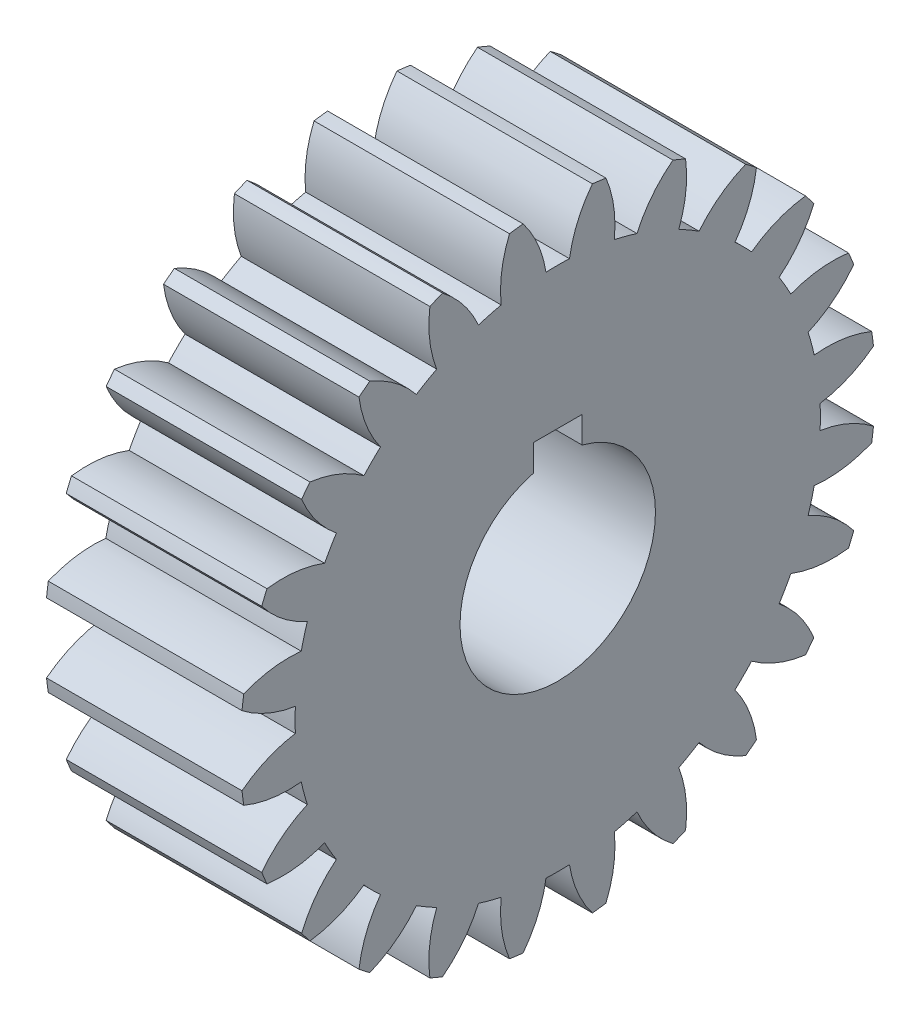
SolidWorks part; units mm, degrees
material "Alumina"
ref_plane "Plane1" through (0, 0, 0) normal (0, 0, 1) x (1, 0, 0)
ref_plane "Plane2" through (0, 0, 0) normal (0, 1, 0) x (1, 0, 0)
ref_plane "Plane3" through (0, 0, 0) normal (1, 0, 0) x (0, 0, -1)
sketch "HoldingSke" plane through (0, 0, 0) normal (0, 1, 0) x (1, 0, 0)
  line L0 (0, 0) -> (371.2649, -165.2978)
  line L1 (-15, 0) -> (100, 0) construction
  line L2 (0, 0) -> (-2.1039, 2.3779)
  line L3 (0, 0) -> (-11.863, 4.5341)
  line L4 (0, 0) -> (7.8894, 3.5126)
  line L5 (0, 0) -> (-47.5972, -17.7524)
  line L6 (0, 0) -> (-10.5278, -7.1032)
  line L7 (-2.1039, 2.3779) -> (8.8308, 51.9871)
  line L8 (-76.2, 54.61) -> (-62.3824, 54.61)
  line L9 (-71.009, 38.7566) -> (-53.1078, 45.2721)
  line L10 (-76.2, 71.12) -> (104.1128, 71.12)
  line L11 (0, 0) -> (-12.7, 0)
  line L12 (-76.2, 101.6) -> (-76.1428, 101.6)
  line L13 (24.9733, 27.94) -> (52.9518, 28.4284)
  line L14 (24.9733, 27.94) -> (24.9746, 27.94)
  line L15 (24.9733, 27.94) -> (100.4006, 29.5858)
  circle A0 centre (0, 0) radius 6.35
  circle A1 centre (0, 0) radius 17.0644
  circle A2 centre (0, 0) radius 38.1
  circle A3 centre (0, 0) radius 6.35
  dimension "MHD" = 34.1287
  dimension "Hub_dia" = 76.2
  dimension "Bore" = 12.7
  dimension "MBD" = 12.7
  dimension "Num_teeth" = 24
  dimension "Pitch" = 406.4
  dimension "Overall_len" = 50.8
  dimension "Show_teeth" = 24
  dimension "Thickness" = 12.7
  dimension "OAL" = 50.8001
  dimension "T_dim" = 13.8176
  dimension "Ap" = 20
  dimension "H" = 19.05
  dimension "Pitch_radius" = 180.3128
  dimension "Width" = 12.7
  dimension "Backlash" = 0.0571
  dimension "Addendum_fac" = 1
  dimension "Dedendum_fac" = 1.25
  dimension "Clearance_fac" = 0.25
  dimension "Dedendum_add" = 0.0013
sketch "BasProSke" plane through (0, 0, 0) normal (0, 1, 0) x (1, 0, 0)
  line L0 (-10, 0) -> (60, 0) construction
  line L1 (0, 0) -> (0, 20.6375)
  line L2 (0, 0) -> (12.7, 0)
  line L3 (12.7, 0) -> (12.7, 20.6375)
  line L4 (12.7, 20.6375) -> (0, 20.6375)
  dimension "Thickness" = 12.7
  dimension "Diameter" = 41.275
revolve "Base-Revolve" add sketch "BasProSke" angle 360 about L0
sketch "TooCutSke" plane through (0, 0, 0) normal (1, 0, 0) x (0, 0, -1)
  line L1 (0, 0) -> (0, 107) construction
  line L2 (0, 0) -> (-1.3459, 19.0024) construction
  line L3 (0, 0) -> (-4.964, 37.7056) construction
  line L4 (-1.3459, 19.0024) -> (-2.482, 18.8528) construction
  arc A0 (0.7625, 17.0473) -> (-0.7625, 17.0473) centre (0, 0) ccw
  arc A1 (2.2707, 20.5378) -> (-2.2707, 20.5378) centre (0, 0) ccw
  circle A2 centre (0, 0) radius 19.05 construction
  circle A3 centre (0, 0) radius 17.9011 construction
  arc A4 (-0.7625, 17.0473) -> (-2.2707, 20.5378) centre (-8.2904, 15.8657) ccw
  arc A5 (2.2707, 20.5378) -> (0.7625, 17.0473) centre (8.2904, 15.8657) ccw
  dimension "Root_dia" = 34.1287
  dimension "Overcut_dia" = 41.3258
  dimension "Pitch_dia" = 38.1
  dimension "Base_dia" = 35.8023
  dimension "Flank_rad" = 7.62
  dimension "Half_ang" = 7.5
  dimension "Half_CT" = 1.1459
extrude "ToothCut" cut sketch "TooCutSke" along normal through all
fillet "Breaks" [suppressed] radius 0.0318
fillet "RootFillets" [suppressed] radius 0.3981
pattern_circular "TeethCuts" count 24 over 360 about axis through (0, 0, 0) along (1, 0, 0) of "ToothCut", "RootFillets", "Breaks"
sketch "HubNeaOneSke" plane through (0, 0, 0) normal (-1, 0, 0) x (0, 0, 1)
  circle A0 centre (0, 0) radius 17.0644
  dimension "Diameter" = 34.1287
extrude "HubNearOne" [suppressed] add sketch "HubNeaOneSke" along normal blind 38.1001
sketch "HubNeaBotSke" plane through (0, 0, 0) normal (-1, 0, 0) x (0, 0, 1)
  circle A0 centre (0, 0) radius 17.0644
  dimension "Diameter" = 34.1287
extrude "HubNearBoth" [suppressed] add sketch "HubNeaBotSke" along normal blind 19.05
ref_plane "FarPln" through (12.7, 0, 0) normal (1, 0, 0) x (0, 0, -1)
sketch "HubFarSke" plane through (12.7, 0, 0) normal (1, 0, 0) x (0, 0, -1)
  circle A0 centre (0, 0) radius 17.0644
  dimension "Diameter" = 34.1287
extrude "HubFar" [suppressed] add sketch "HubFarSke" along normal blind 19.05
sketch "BorSke" plane through (0, 0, 0) normal (1, 0, 0) x (0, 0, -1)
  circle A0 centre (0, 0) radius 6.35
  dimension "Diameter" = 12.7
extrude "Bore" cut sketch "BorSke" along normal mid plane 101.6001
sketch "KeySke" plane through (0, 0, 0) normal (1, 0, 0) x (0, 0, -1)
  line L0 (-1.5875, 0) -> (-1.5875, 7.4676)
  line L1 (-1.5875, 7.4676) -> (1.5875, 7.4676)
  line L2 (1.5875, 7.4676) -> (1.5875, 0)
  line L3 (0, 0) -> (0, 34) construction
  line L4 (-1.5875, 0) -> (1.5875, 0)
  dimension "Offset" = 7.4676
  dimension "Width" = 3.175
extrude "Keyway" cut sketch "KeySke" along normal mid plane 101.6001
pattern_circular "Keyway2" [suppressed] count 2 every 90 about axis through (-10, 0, 0) along (1, 0, 0)
sketch "Sketch1" plane through (12.7, 0, 0) normal (1, 0, 0) x (0, 0, -1)
  line L0 (-1.5875, 7.4676) -> (-1.5875, 7.874)
  line L1 (1.5875, 7.4676) -> (1.5875, 7.874)
  line L2 (-1.5875, 7.874) -> (1.5875, 7.874)
extrude "Cut-Extrude3" cut sketch "Sketch1" against normal through all and the other way through all
equation "' \"Pitch@HoldingSke\" = 4"
equation "' \"Num_teeth@HoldingSke\" = 12"
equation "' \"Ap@HoldingSke\" =  20"
equation "' \"Ap@HoldingSke\" = 20"
equation "' \"Width@HoldingSke\" = 0.5"
equation "' \"Hub_dia@HoldingSke\"= 1"
equation "' \"Hub_dia@HoldingSke\" = 1"
equation "' \"Overall_len@HoldingSke\" = 1.0"
equation "' \"Bore@HoldingSke\" = 0.75"
equation "' \"T_dim@HoldingSke\" = 0.85"
equation "' \"Width@KeySke\" = 0.25"
equation "' \"Show_teeth@HoldingSke\" = 13"
equation "' \"Backlash@HoldingSke\" = 0.009"
equation "' \"Addendum_fac@HoldingSke\" = 1.0"
equation "' \"Dedendum_fac@HoldingSke\" = 1.25"
equation "' \"Dedendum_add@HoldingSke\" = 0.00005"
equation "' \"Clearance_fac@HoldingSke\" = 0.25"
equation "' \"Pitch@HoldingSke\" = 0.5"
equation "' \"Num_teeth@HoldingSke\" = 23"
equation "' \"Show_teeth@HoldingSke\" = 23"
equation "' \"Backlash@HoldingSke\" = 0.0375"
equation "\"Overcut_dia@TooCutSke\" = (\"Num_teeth@HoldingSke\" + 2 * \"Addendum_fac@HoldingSke\") / \"Pitch@HoldingSke\" + 0.002"
equation "\"Pitch_dia@TooCutSke\" = \"Num_teeth@HoldingSke\" / \"Pitch@HoldingSke\""
equation "\"Base_dia@TooCutSke\" = \"Num_teeth@HoldingSke\" / \"Pitch@HoldingSke\" * cos((\"Ap@HoldingSke\"  * 3.14159265 / 180))"
equation "\"Root_dia@TooCutSke\" = (\"Num_teeth@HoldingSke\" + 2) / \"Pitch@HoldingSke\" - 2 * (\"Addendum_fac@HoldingSke\" + \"Dedendum_fac@HoldingSke\") / \"Pitch@HoldingSke\" - \"Dedendum_add@HoldingSke\" * 2"
equation "\"Half_ang@TooCutSke\" = 180 / \"Num_teeth@HoldingSke\""
equation "\"Half_CT@TooCutSke\" = \"Num_teeth@HoldingSke\" / \"Pitch@HoldingSke\" * sin((3.14159265 / 2 / \"Num_teeth@HoldingSke\")) / 2 - 7 * \"Backlash@HoldingSke\" / 4"
equation "\"Flank_rad@TooCutSke\" = \"Num_teeth@HoldingSke\" / \"Pitch@HoldingSke\" / 5"
equation "\"Radius@RootFillets\" = \"Clearance_fac@HoldingSke\" / \"Pitch@HoldingSke\" + \"Dedendum_add@HoldingSke\""
equation "\"Break_rad@Breaks\" = 0.02 / \"Pitch@HoldingSke\""
equation "\"Thickness@HoldingSke\" = \"Width@HoldingSke\""
equation "\"OAL@HoldingSke\" = \"Thickness@HoldingSke\""
equation "\"MHD@HoldingSke\" = (\"Num_teeth@HoldingSke\" + 2) / \"Pitch@HoldingSke\" - 2 * (\"Addendum_fac@HoldingSke\" + \"Dedendum_fac@HoldingSke\")  / \"Pitch@HoldingSke\" - \"Dedendum_add@HoldingSke\" * 2"
equation "\"MBD@HoldingSke\" = (\"Num_teeth@HoldingSke\" + 2) / \"Pitch@HoldingSke\" - 2 * (\"Addendum_fac@HoldingSke\" + \"Dedendum_fac@HoldingSke\")  / \"Pitch@HoldingSke\" - \"Dedendum_add@HoldingSke\" * 2 - 0.002"
equation "\"MHD@HoldingSke\" = ((sgn( \"MHD@HoldingSke\" - \"Hub_dia@HoldingSke\" )-1)*( \"MHD@HoldingSke\" - \"Hub_dia@HoldingSke\" ))/-2+ \"Hub_dia@HoldingSke\""
equation "\"MBD@HoldingSke\" = ((sgn( \"MBD@HoldingSke\" - \"Bore@HoldingSke\" )-1)*( \"MBD@HoldingSke\" - \"Bore@HoldingSke\" ))/-2+ \"Bore@HoldingSke\""
equation "\"OAL@HoldingSke\" = ((sgn( \"OAL@HoldingSke\" - \"Overall_len@HoldingSke\" )+1)*( \"OAL@HoldingSke\" - \"Overall_len@HoldingSke\" ))/2 + \"Overall_len@HoldingSke\" + 0.000002"
equation "\"Num_teeth@TeethCuts\" = int( \"Show_teeth@HoldingSke\" ) + 1"
equation "\"Num_teeth@TeethCuts\" = ((sgn( \"Num_teeth@TeethCuts\" - \"Num_teeth@HoldingSke\" )-1)*( \"Num_teeth@TeethCuts\" - \"Num_teeth@HoldingSke\" ))/-2+ \"Num_teeth@HoldingSke\""
equation "\"Num_teeth@TeethCuts\" = ((sgn( \"Num_teeth@TeethCuts\" - 2.0)+1)*( \"Num_teeth@TeethCuts\" - 2.0))/2 +2.0"
equation "\"Angle@TeethCuts\" = 360.0 / \"Num_teeth@HoldingSke\""
equation "\"Diameter@BasProSke\" = (\"Num_teeth@HoldingSke\" + 2 * \"Addendum_fac@HoldingSke\") / \"Pitch@HoldingSke\""
equation "\"Thickness@BasProSke\"  = \"Thickness@HoldingSke\""
equation "' \"Fillet_rad@BasProSke\" =  \"Thickness@HoldingSke\" * 0.05"
equation "' \"Fillet_rad@BasProSke\" = \"Thickness@HoldingSke\" * 0.05"
equation "\"MHD@HoldingSke\" = ((sgn( \"MHD@HoldingSke\" - \"Root_dia@TooCutSke\" )-1)*( \"MHD@HoldingSke\" - \"Root_dia@TooCutSke\" ))/-2+ \"Root_dia@TooCutSke\""
equation "\"Diameter@HubNeaOneSke\" = \"MHD@HoldingSke\""
equation "\"Length@HubNearOne\" = \"OAL@HoldingSke\" - \"Thickness@BasProSke\""
equation "\"Diameter@HubNeaBotSke\" = \"MHD@HoldingSke\""
equation "\"Length@HubNearBoth\" = ( \"OAL@HoldingSke\" - \"Thickness@BasProSke\" ) / 2.0"
equation "\"Thickness@FarPln\" = \"Thickness@BasProSke\""
equation "\"Diameter@HubFarSke\" = \"MHD@HoldingSke\""
equation "\"Length@HubFar\" = ( \"OAL@HoldingSke\" - \"Thickness@BasProSke\" ) / 2.0"
equation "\"Diameter@BorSke\" = \"MBD@HoldingSke\""
equation "\"D1@Bore\" = \"OAL@HoldingSke\" * 2.0"
equation "\"D1@Keyway\" = \"OAL@HoldingSke\" * 2.0"
equation "\"Offset@KeySke\" = \"T_dim@HoldingSke\" - \"MBD@HoldingSke\" / 2.0"
